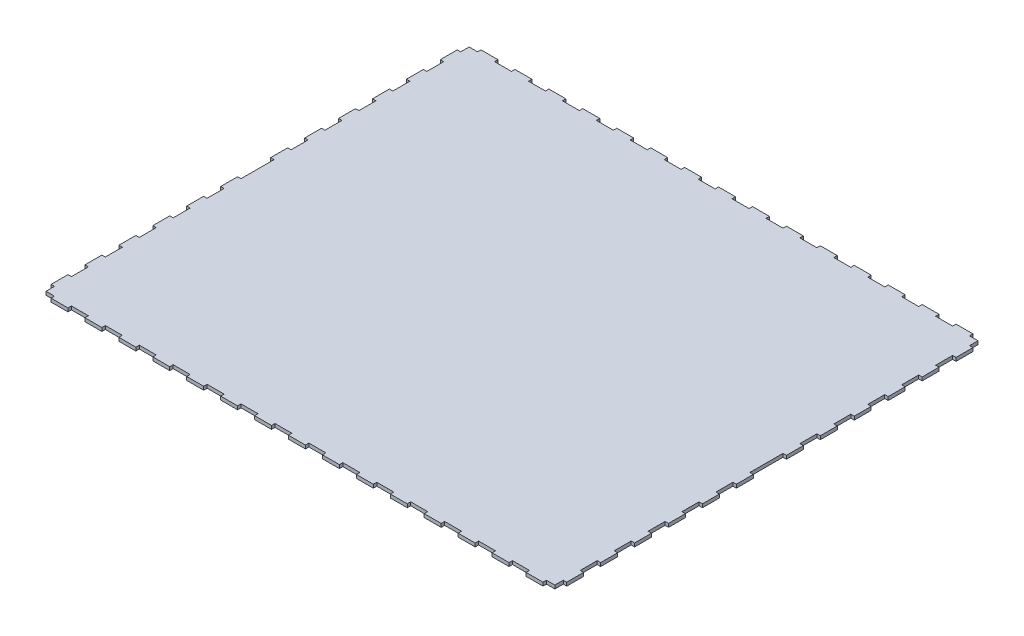
SolidWorks part; units mm, degrees
ref_plane "Front Plane" through (0, 0, 0) normal (0, 0, 1) x (1, 0, 0)
ref_plane "Top Plane" through (0, 0, 0) normal (0, 1, 0) x (1, 0, 0)
ref_plane "Right Plane" through (0, 0, 0) normal (1, 0, 0) x (0, 0, -1)
sketch "Sketch1" plane through (0, 0, 0) normal (0, 1, 0) x (1, 0, 0)
  line L0 (0, 0) -> (0, 393.7676) construction
  line L1 (9.8625, 250) -> (-9.8625, 250)
  line L2 (9.8625, 250) -> (9.8625, 246)
  line L3 (9.8625, 246) -> (29.5875, 246)
  line L4 (29.5875, 246) -> (29.5875, 250)
  line L5 (29.5875, 250) -> (49.3125, 250)
  line L6 (49.3125, 250) -> (49.3125, 246)
  line L7 (49.3125, 246) -> (69.0375, 246)
  line L8 (69.0375, 246) -> (69.0375, 250)
  line L9 (69.0375, 250) -> (88.7625, 250)
  line L10 (88.7625, 250) -> (88.7625, 246)
  line L11 (88.7625, 246) -> (108.4875, 246)
  line L12 (108.4875, 246) -> (108.4875, 250)
  line L13 (108.4875, 250) -> (128.2125, 250)
  line L14 (128.2125, 250) -> (128.2125, 246)
  line L15 (128.2125, 246) -> (147.9375, 246)
  line L16 (147.9375, 246) -> (147.9375, 250)
  line L17 (147.9375, 250) -> (167.6625, 250)
  line L18 (167.6625, 250) -> (167.6625, 246)
  line L19 (167.6625, 246) -> (187.3875, 246)
  line L20 (187.3875, 246) -> (187.3875, 250)
  line L21 (187.3875, 250) -> (207.1125, 250)
  line L22 (207.1125, 250) -> (207.1125, 246)
  line L23 (207.1125, 246) -> (226.8375, 246)
  line L24 (226.8375, 246) -> (226.8375, 250)
  line L25 (226.8375, 250) -> (246.5625, 250)
  line L26 (246.5625, 250) -> (246.5625, 246)
  line L27 (246.5625, 246) -> (266.2875, 246)
  line L28 (266.2875, 246) -> (266.2875, 250)
  line L29 (266.2875, 250) -> (286.0125, 250)
  line L30 (286.0125, 250) -> (286.0125, 246)
  line L31 (286.0125, 246) -> (295.8125, 246)
  line L32 (-286.0125, 246) -> (-295.8125, 246)
  line L33 (-286.0125, 250) -> (-286.0125, 246)
  line L34 (-266.2875, 250) -> (-286.0125, 250)
  line L35 (-266.2875, 246) -> (-266.2875, 250)
  line L36 (-246.5625, 246) -> (-266.2875, 246)
  line L37 (-246.5625, 250) -> (-246.5625, 246)
  line L38 (-226.8375, 250) -> (-246.5625, 250)
  line L39 (-226.8375, 246) -> (-226.8375, 250)
  line L40 (-207.1125, 246) -> (-226.8375, 246)
  line L41 (-207.1125, 250) -> (-207.1125, 246)
  line L42 (-187.3875, 250) -> (-207.1125, 250)
  line L43 (-187.3875, 246) -> (-187.3875, 250)
  line L44 (-167.6625, 246) -> (-187.3875, 246)
  line L45 (-167.6625, 250) -> (-167.6625, 246)
  line L46 (-147.9375, 250) -> (-167.6625, 250)
  line L47 (-147.9375, 246) -> (-147.9375, 250)
  line L48 (-128.2125, 246) -> (-147.9375, 246)
  line L49 (-128.2125, 250) -> (-128.2125, 246)
  line L50 (-108.4875, 250) -> (-128.2125, 250)
  line L51 (-108.4875, 246) -> (-108.4875, 250)
  line L52 (-88.7625, 246) -> (-108.4875, 246)
  line L53 (-88.7625, 250) -> (-88.7625, 246)
  line L54 (-69.0375, 250) -> (-88.7625, 250)
  line L55 (-69.0375, 246) -> (-69.0375, 250)
  line L56 (-49.3125, 246) -> (-69.0375, 246)
  line L57 (-49.3125, 250) -> (-49.3125, 246)
  line L58 (-29.5875, 250) -> (-49.3125, 250)
  line L59 (-29.5875, 246) -> (-29.5875, 250)
  line L60 (-9.8625, 246) -> (-29.5875, 246)
  line L61 (-9.8625, 250) -> (-9.8625, 246)
  line L62 (295.8125, 246) -> (295.8125, 236.2)
  line L63 (295.8125, 236.2) -> (299.8125, 236.2)
  line L64 (299.8125, 236.2) -> (299.8125, 216.475)
  line L65 (299.8125, 216.475) -> (295.8125, 216.475)
  line L66 (295.8125, 216.475) -> (295.8125, 196.75)
  line L67 (299.8125, 196.75) -> (299.8125, 177.025)
  line L68 (299.8125, 177.025) -> (295.8125, 177.025)
  line L69 (295.8125, 196.75) -> (299.8125, 196.75)
  line L70 (295.8125, 177.025) -> (295.8125, 157.3)
  line L71 (299.8125, 157.3) -> (299.8125, 137.575)
  line L72 (299.8125, 137.575) -> (295.8125, 137.575)
  line L73 (295.8125, 157.3) -> (299.8125, 157.3)
  line L74 (295.8125, 137.575) -> (295.8125, 117.85)
  line L75 (299.8125, 117.85) -> (299.8125, 98.125)
  line L76 (299.8125, 98.125) -> (295.8125, 98.125)
  line L77 (295.8125, 117.85) -> (299.8125, 117.85)
  line L78 (295.8125, 98.125) -> (295.8125, 78.4)
  line L79 (299.8125, 78.4) -> (299.8125, 58.675)
  line L80 (299.8125, 58.675) -> (295.8125, 58.675)
  line L81 (295.8125, 78.4) -> (299.8125, 78.4)
  line L82 (299.8125, 38.95) -> (299.8125, 19.225)
  line L83 (0, 0) -> (349.1391, 0) construction
  line L84 (299.8125, 19.225) -> (295.8125, 19.225)
  line L85 (295.8125, 19.225) -> (295.8125, -19.225)
  line L93 (-295.8125, 38.95) -> (-295.8125, 58.675)
  line L94 (-295.8125, 38.95) -> (-299.8125, 38.95)
  line L95 (-295.8125, 19.225) -> (-295.8125, -19.225)
  line L96 (-299.8125, 19.225) -> (-295.8125, 19.225)
  line L97 (-299.8125, 38.95) -> (-299.8125, 19.225)
  line L98 (-295.8125, 78.4) -> (-299.8125, 78.4)
  line L99 (-299.8125, 58.675) -> (-295.8125, 58.675)
  line L100 (-299.8125, 78.4) -> (-299.8125, 58.675)
  line L101 (-295.8125, 98.125) -> (-295.8125, 78.4)
  line L102 (-295.8125, 117.85) -> (-299.8125, 117.85)
  line L103 (-299.8125, 98.125) -> (-295.8125, 98.125)
  line L104 (-299.8125, 117.85) -> (-299.8125, 98.125)
  line L105 (295.8125, 38.95) -> (299.8125, 38.95)
  line L106 (295.8125, 58.675) -> (295.8125, 38.95) [skipped]
  line L107 (-295.8125, 137.575) -> (-295.8125, 117.85)
  line L108 (-295.8125, 157.3) -> (-299.8125, 157.3)
  line L109 (-299.8125, 137.575) -> (-295.8125, 137.575)
  line L110 (-299.8125, 157.3) -> (-299.8125, 137.575)
  line L111 (-295.8125, 177.025) -> (-295.8125, 157.3)
  line L112 (-295.8125, 196.75) -> (-299.8125, 196.75)
  line L113 (-299.8125, 177.025) -> (-295.8125, 177.025)
  line L114 (-299.8125, 196.75) -> (-299.8125, 177.025)
  line L115 (-295.8125, 216.475) -> (-295.8125, 196.75)
  line L116 (295.8125, 38.95) -> (295.8125, 58.675)
  line L117 (-299.8125, 216.475) -> (-295.8125, 216.475)
  line L118 (295.8125, -59.675) -> (295.8125, -79.4) [skipped]
  line L119 (295.8125, 19.225) -> (295.8125, -0.5) [skipped]
  line L120 (299.8125, -0.5) -> (299.8125, -20.225) [skipped]
  line L121 (299.8125, -20.225) -> (295.8125, -20.225) [skipped]
  line L122 (295.8125, -0.5) -> (299.8125, -0.5) [skipped]
  line L123 (295.8125, -20.225) -> (295.8125, -39.95) [skipped]
  line L124 (299.8125, -39.95) -> (299.8125, -59.675) [skipped]
  line L125 (299.8125, -59.675) -> (295.8125, -59.675) [skipped]
  line L126 (295.8125, -39.95) -> (299.8125, -39.95) [skipped]
  line L127 (-299.8125, 236.2) -> (-299.8125, 216.475)
  line L128 (-295.8125, 236.2) -> (-299.8125, 236.2)
  line L129 (-295.8125, 246) -> (-295.8125, 236.2)
  line L131 (-295.8125, -246) -> (-295.8125, -236.2)
  line L132 (-295.8125, -236.2) -> (-299.8125, -236.2)
  line L133 (-299.8125, -236.2) -> (-299.8125, -216.475)
  line L134 (-299.8125, -216.475) -> (-295.8125, -216.475)
  line L135 (295.8125, -38.95) -> (295.8125, -58.675)
  line L136 (-295.8125, -216.475) -> (-295.8125, -196.75)
  line L137 (-299.8125, -196.75) -> (-299.8125, -177.025)
  line L138 (-299.8125, -177.025) -> (-295.8125, -177.025)
  line L139 (-295.8125, -196.75) -> (-299.8125, -196.75)
  line L140 (-295.8125, -177.025) -> (-295.8125, -157.3)
  line L141 (-299.8125, -157.3) -> (-299.8125, -137.575)
  line L142 (-299.8125, -137.575) -> (-295.8125, -137.575)
  line L143 (-295.8125, -157.3) -> (-299.8125, -157.3)
  line L144 (-295.8125, -137.575) -> (-295.8125, -117.85)
  line L145 (295.8125, -38.95) -> (299.8125, -38.95)
  line L146 (-299.8125, -117.85) -> (-299.8125, -98.125)
  line L147 (-299.8125, -98.125) -> (-295.8125, -98.125)
  line L148 (-295.8125, -117.85) -> (-299.8125, -117.85)
  line L149 (-295.8125, -98.125) -> (-295.8125, -78.4)
  line L150 (-299.8125, -78.4) -> (-299.8125, -58.675)
  line L151 (-299.8125, -58.675) -> (-295.8125, -58.675)
  line L152 (-295.8125, -78.4) -> (-299.8125, -78.4)
  line L153 (-299.8125, -38.95) -> (-299.8125, -19.225)
  line L154 (-299.8125, -19.225) -> (-295.8125, -19.225)
  line L155 (-295.8125, -38.95) -> (-299.8125, -38.95)
  line L156 (-295.8125, -38.95) -> (-295.8125, -58.675)
  line L157 (299.8125, -19.225) -> (295.8125, -19.225)
  line L158 (299.8125, -38.95) -> (299.8125, -19.225)
  line L159 (295.8125, -78.4) -> (299.8125, -78.4)
  line L160 (299.8125, -58.675) -> (295.8125, -58.675)
  line L161 (299.8125, -78.4) -> (299.8125, -58.675)
  line L162 (295.8125, -98.125) -> (295.8125, -78.4)
  line L163 (295.8125, -117.85) -> (299.8125, -117.85)
  line L164 (299.8125, -98.125) -> (295.8125, -98.125)
  line L165 (299.8125, -117.85) -> (299.8125, -98.125)
  line L166 (295.8125, -137.575) -> (295.8125, -117.85)
  line L167 (295.8125, -157.3) -> (299.8125, -157.3)
  line L168 (299.8125, -137.575) -> (295.8125, -137.575)
  line L169 (299.8125, -157.3) -> (299.8125, -137.575)
  line L170 (295.8125, -177.025) -> (295.8125, -157.3)
  line L171 (295.8125, -196.75) -> (299.8125, -196.75)
  line L172 (299.8125, -177.025) -> (295.8125, -177.025)
  line L173 (299.8125, -196.75) -> (299.8125, -177.025)
  line L174 (295.8125, -216.475) -> (295.8125, -196.75)
  line L175 (299.8125, -216.475) -> (295.8125, -216.475)
  line L176 (299.8125, -236.2) -> (299.8125, -216.475)
  line L177 (295.8125, -236.2) -> (299.8125, -236.2)
  line L178 (295.8125, -246) -> (295.8125, -236.2)
  line L179 (-9.8625, -250) -> (-9.8625, -246)
  line L180 (-9.8625, -246) -> (-29.5875, -246)
  line L181 (-29.5875, -246) -> (-29.5875, -250)
  line L182 (-29.5875, -250) -> (-49.3125, -250)
  line L183 (-49.3125, -250) -> (-49.3125, -246)
  line L184 (-49.3125, -246) -> (-69.0375, -246)
  line L185 (-69.0375, -246) -> (-69.0375, -250)
  line L186 (-69.0375, -250) -> (-88.7625, -250)
  line L187 (-88.7625, -250) -> (-88.7625, -246)
  line L188 (-88.7625, -246) -> (-108.4875, -246)
  line L189 (-108.4875, -246) -> (-108.4875, -250)
  line L190 (-108.4875, -250) -> (-128.2125, -250)
  line L191 (-128.2125, -250) -> (-128.2125, -246)
  line L192 (-128.2125, -246) -> (-147.9375, -246)
  line L193 (-147.9375, -246) -> (-147.9375, -250)
  line L194 (-147.9375, -250) -> (-167.6625, -250)
  line L195 (-167.6625, -250) -> (-167.6625, -246)
  line L196 (-167.6625, -246) -> (-187.3875, -246)
  line L197 (-187.3875, -246) -> (-187.3875, -250)
  line L198 (-187.3875, -250) -> (-207.1125, -250)
  line L199 (-207.1125, -250) -> (-207.1125, -246)
  line L200 (-207.1125, -246) -> (-226.8375, -246)
  line L201 (-226.8375, -246) -> (-226.8375, -250)
  line L202 (-226.8375, -250) -> (-246.5625, -250)
  line L203 (-246.5625, -250) -> (-246.5625, -246)
  line L204 (-246.5625, -246) -> (-266.2875, -246)
  line L205 (-266.2875, -246) -> (-266.2875, -250)
  line L206 (-266.2875, -250) -> (-286.0125, -250)
  line L207 (-286.0125, -250) -> (-286.0125, -246)
  line L208 (-286.0125, -246) -> (-295.8125, -246)
  line L209 (286.0125, -246) -> (295.8125, -246)
  line L210 (286.0125, -250) -> (286.0125, -246)
  line L211 (266.2875, -250) -> (286.0125, -250)
  line L212 (266.2875, -246) -> (266.2875, -250)
  line L213 (246.5625, -246) -> (266.2875, -246)
  line L214 (246.5625, -250) -> (246.5625, -246)
  line L215 (226.8375, -250) -> (246.5625, -250)
  line L216 (226.8375, -246) -> (226.8375, -250)
  line L217 (207.1125, -246) -> (226.8375, -246)
  line L218 (207.1125, -250) -> (207.1125, -246)
  line L219 (187.3875, -250) -> (207.1125, -250)
  line L220 (187.3875, -246) -> (187.3875, -250)
  line L221 (167.6625, -246) -> (187.3875, -246)
  line L222 (167.6625, -250) -> (167.6625, -246)
  line L223 (147.9375, -250) -> (167.6625, -250)
  line L224 (147.9375, -246) -> (147.9375, -250)
  line L225 (128.2125, -246) -> (147.9375, -246)
  line L226 (128.2125, -250) -> (128.2125, -246)
  line L227 (108.4875, -250) -> (128.2125, -250)
  line L228 (108.4875, -246) -> (108.4875, -250)
  line L229 (88.7625, -246) -> (108.4875, -246)
  line L230 (88.7625, -250) -> (88.7625, -246)
  line L231 (69.0375, -250) -> (88.7625, -250)
  line L232 (69.0375, -246) -> (69.0375, -250)
  line L233 (49.3125, -246) -> (69.0375, -246)
  line L234 (49.3125, -250) -> (49.3125, -246)
  line L235 (29.5875, -250) -> (49.3125, -250)
  line L236 (29.5875, -246) -> (29.5875, -250)
  line L237 (9.8625, -246) -> (29.5875, -246)
  line L238 (9.8625, -250) -> (9.8625, -246)
  line L239 (9.8625, -250) -> (-9.8625, -250)
  point P66 (0, 250)
  point P67 (0, 250)
  point P96 (0, 25)
  point P166 (-295.8125, 0)
  point P168 (295.8125, 0)
  point P249 (0, -25)
  point P250 (0, -250)
  dimension "D1" = 9.8625
  dimension "D2" = 19.725
  dimension "D3" = 4
  dimension "D4" = 246
  dimension "D5" = 7
  dimension "D6" = 9.8
  dimension "D7" = 8
extrude "Boss-Extrude1" add sketch "Sketch1" along normal blind 4
